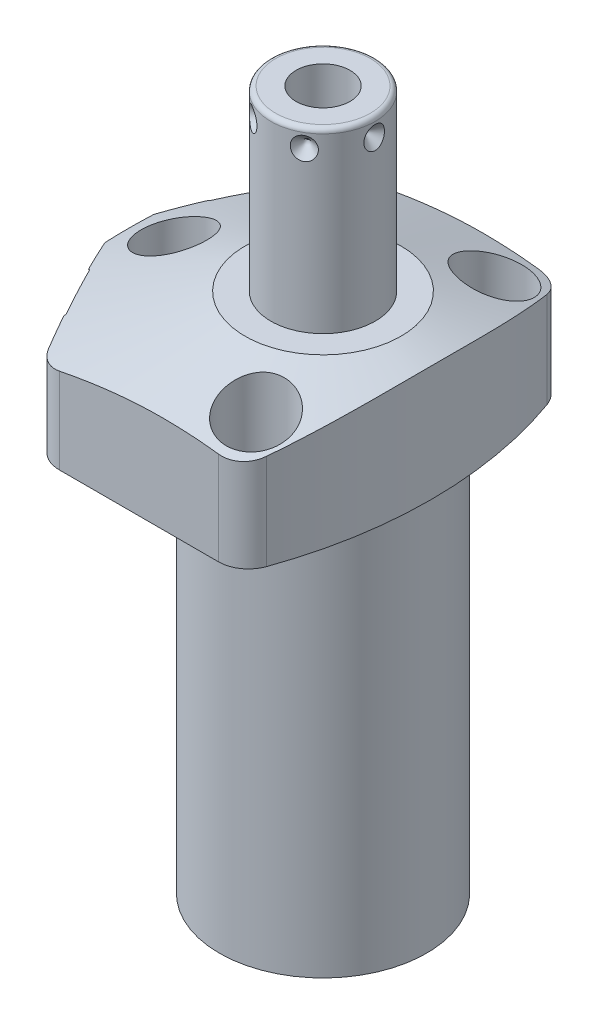
SolidWorks part; units mm, degrees
material "Alloy Steel"
ref_plane "Front Plane" through (0, 0, 0) normal (0, 0, 1) x (1, 0, 0)
ref_plane "Top Plane" through (0, 0, 0) normal (0, 1, 0) x (1, 0, 0)
ref_plane "Right Plane" through (0, 0, 0) normal (1, 0, 0) x (0, 0, -1)
ref_plane "Plane1" through (0, 0, 0) normal (0, 0, 1) x (0, -1, 0)
sketch "Sketch1" plane through (0, 0, 0) normal (0, 0, 1) x (0, -1, 0)
  line L0 (0, 44.45) -> (-26.9748, 44.45)
  line L1 (-26.9748, 44.45) -> (-26.9748, 0)
  line L2 (-26.9748, 0) -> (84.1502, 0)
  line L3 (84.1502, 0) -> (84.1502, 22.098)
  line L4 (84.1502, 22.098) -> (0, 22.098)
  line L5 (0, 22.098) -> (0, 44.45)
  line L6 (-32.531, 0) -> (89.7065, 0) construction
  dimension "D1" = 111.125
  dimension "D2" = 26.9748
  dimension "D3" = 88.9
  dimension "D4" = 44.196
revolve "Revolve1" add sketch "Sketch1" angle 360 about L6
ref_plane "Plane2" through (0, 0, 0) normal (0, -1, 0) x (0, 0, -1)
sketch "Sketch2" plane through (0, 0, 0) normal (0, -1, 0) x (0, 0, -1)
  line L0 (34.1122, -28.4984) -> (34.1122, 28.4984)
  line L2 (-34.1122, 28.4984) -> (-34.1122, -28.4984)
  line L3 (0, -32.1458) -> (0, 48.0974) construction
  arc A0 (34.1122, -28.4984) -> (34.1122, 28.4984) centre (0, 0) ccw
  circle A1 centre (0, 0) radius 44.45
  arc A2 (-34.1122, 28.4984) -> (-34.1122, -28.4984) centre (0, 0) ccw
  point P4 (0, 0)
  dimension "D1" = 68.2244
  dimension "D2" = 0
extrude "Cut-Extrude1" cut sketch "Sketch2" against normal up to next
ref_plane "Plane3" through (0, 0, 0) normal (0, -1, 0) x (-1, 0, 0)
sketch "Sketch3" plane through (0, 0, 0) normal (0, -1, 0) x (-1, 0, 0)
  line L0 (25.9049, 34.1122) -> (44.0427, 0)
  line L1 (44.0427, 0) -> (25.9049, -34.1122)
  line L2 (-39.4859, -20.995) -> (73.8214, 39.2515) construction
  line L3 (0, 0) -> (44.0427, 0) construction
  line L6 (-28.4984, -34.1122) -> (28.4984, -34.1122)
  line L7 (28.4984, 34.1122) -> (-28.4984, 34.1122)
  line L8 (25.9049, -34.1122) -> (28.4984, -34.1122)
  line L9 (28.4984, 34.1122) -> (25.9049, 34.1122)
  arc A2 (-28.4984, 34.1122) -> (-28.4984, -34.1122) centre (0, 0) ccw
  arc A3 (28.4984, -34.1122) -> (28.4984, 34.1122) centre (0, 0) ccw
  arc A5 (28.4984, -34.1122) -> (28.4984, 34.1122) centre (0, 0) ccw
  dimension "D1" = 28
  dimension "D2" = 38.8874
  dimension "D3" = 0
extrude "Cut-Extrude2" cut sketch "Sketch3" against normal up to next
ref_plane "Plane4" through (0, 0, 0) normal (0, -1, 0) x (-1, 0, 0)
sketch "S2D0002" plane through (0, 0, 0) normal (0, -1, 0) x (-1, 0, 0)
  line L0 (41.275, 85.425) -> (41.275, -85.425)
  arc A0 (41.275, 85.425) -> (41.275, -85.425) centre (65.8876, 0) ccw
  dimension "D3" = 88.9
  dimension "D1" = 65.8876
  dimension "D2" = 41.275
extrude "Cut-Extrude3" cut sketch "S2D0002" against normal blind 38.0873 flip side to cut
fillet "Fillet1" radius 6.35 2 edges at (16.2073, 13.4874, 34.1122) (16.2073, 13.4874, -34.1122)
fillet "Fillet2" radius 6.35 1 edges at (-25.9049, 13.4874, 34.1122)
fillet "Fillet3" radius 6.35 1 edges at (-25.9049, 13.4874, -34.1122)
ref_plane "Plane5" through (0, 0, 0) normal (0, 0, 1) x (1, 0, 0)
sketch "Sketch5" plane through (0, 0, 0) normal (0, 0, 1) x (1, 0, 0)
  line L0 (-16.637, 26.9748) -> (-47.625, 15.6961)
  line L1 (0, 7.6649) -> (0, 27.5963) construction
  line L3 (11.854, 26.9748) -> (-22.0895, 26.9748) construction
  line L4 (-16.637, 26.9748) -> (-47.625, 26.9748)
  line L5 (-47.625, 26.9748) -> (-47.625, 15.6961)
  dimension "D1" = 33.274
  dimension "D2" = 20
  dimension "D3" = 47.625
revolve "Cut-Revolve1" cut sketch "Sketch5" angle 360 about L1
ref_plane "Plane6" through (-34.1113, 10.287, -18.1373) normal (0, 1, 0) x (0.4695, 0, -0.8829)
sketch "Sketch6" plane through (-34.1113, 10.287, -18.1373) normal (0, 1, 0) x (0.4695, 0, -0.8829)
  line L0 (0, 0) -> (6.1849, 0)
  line L1 (6.1849, 0) -> (5.6423, -2.5527)
  line L2 (5.6423, -2.5527) -> (4.9784, -3.2166)
  line L3 (4.9784, -3.2166) -> (4.9784, -15.748)
  line L4 (4.9784, -15.748) -> (0, -15.748)
  line L5 (0, -15.748) -> (0, 0)
  line L6 (0, -16.5354) -> (0, 0.7874) construction
  dimension "D1" = 15.748
revolve "Cut-Revolve2" cut sketch "Sketch6" angle 360 about L6
ref_plane "Plane7" through (-34.1113, 10.287, 18.1373) normal (0, 1, 0) x (-0.4695, 0, -0.8829)
sketch "Sketch7" plane through (-34.1113, 10.287, 18.1373) normal (0, 1, 0) x (-0.4695, 0, -0.8829)
  line L0 (0, 0) -> (6.1849, 0)
  line L1 (6.1849, 0) -> (5.6423, -2.5527)
  line L2 (5.6423, -2.5527) -> (4.9784, -3.2166)
  line L3 (4.9784, -3.2166) -> (4.9784, -15.748)
  line L4 (4.9784, -15.748) -> (0, -15.748)
  line L5 (0, -15.748) -> (0, 0)
  line L6 (0, -16.5354) -> (0, 0.7874) construction
  dimension "D1" = 15.748
revolve "Cut-Revolve3" cut sketch "Sketch7" angle 360 about L6
ref_plane "Plane8" through (-13.4874, 2.667, -26.5938) normal (0, 0, 1) x (-1, 0, 0)
sketch "Sketch8" plane through (-13.4874, 2.667, -26.5938) normal (0, 0, 1) x (-1, 0, 0)
  line L0 (0, 0) -> (4.5466, 0)
  line L1 (4.5466, 0) -> (4.1066, -2.0701)
  line L2 (4.1066, -2.0701) -> (3.4544, -2.7223)
  line L3 (3.4544, -2.7223) -> (3.4544, -12.573)
  line L4 (3.4544, -12.573) -> (0, -12.573)
  line L5 (0, -12.573) -> (0, 0)
  line L6 (0, -13.2017) -> (0, 0.6287) construction
  dimension "D1" = 12.573
revolve "Cut-Revolve4" cut sketch "Sketch8" angle 360 about L6
ref_plane "Plane9" through (-13.4874, 2.667, 26.5938) normal (0, 0, 1) x (-1, 0, 0)
sketch "Sketch9" plane through (-13.4874, 2.667, 26.5938) normal (0, 0, 1) x (-1, 0, 0)
  line L0 (0, 0) -> (4.5466, 0)
  line L1 (4.5466, 0) -> (4.1066, -2.0701)
  line L2 (4.1066, -2.0701) -> (3.4544, -2.7223)
  line L3 (3.4544, -2.7223) -> (3.4544, -12.573)
  line L4 (3.4544, -12.573) -> (0, -12.573)
  line L5 (0, -12.573) -> (0, 0)
  line L6 (0, -13.2017) -> (0, 0.6287) construction
  dimension "D1" = 12.573
revolve "Cut-Revolve5" cut sketch "Sketch9" angle 360 about L6
sketch "Sketch17" plane through (-34.3355, 0, 18.2565) normal (-0.8829, 0, 0.4695) x (0.4695, 0, 0.8829)
  circle A0 centre (0, 10.287) radius 10.4775
  dimension "D1" = 20.955
extrude "Cut-Extrude4" cut sketch "Sketch17" against normal blind 0.254
sketch "Sketch18" plane through (0, 0, 0) normal (0, -1, 0) x (1, 0, 0)
  circle A0 centre (-13.4874, 26.5938) radius 5.5626
  dimension "D1" = 11.1252
extrude "Cut-Extrude5" cut sketch "Sketch18" against normal blind 2.667
mirror "Mirror1" about plane through (0, 0, 0) normal (0, 0, 1) of "Cut-Extrude5", "Cut-Extrude4"
ref_plane "Plane10" through (0, 0, 0) normal (1, 0, 0) x (0, 0, -1)
sketch "Sketch10" plane through (0, 0, 0) normal (1, 0, 0) x (0, 0, -1)
  line L0 (0, 26.9748) -> (-11.1125, 26.9748)
  line L1 (-11.1125, 26.9748) -> (-11.1125, 63.8302)
  line L2 (-10.0965, 64.8462) -> (0, 64.8462)
  line L3 (0, 64.8462) -> (0, 26.9748)
  line L4 (0, 14.3517) -> (0, 66.7398) construction
  line L5 (16.637, 26.9748) -> (-16.637, 26.9748) construction
  line L6 (-29.8978, 0) -> (29.8978, 0) construction
  arc A0 (-10.0965, 64.8462) -> (-11.1125, 63.8302) centre (-10.0965, 63.8302) ccw
  dimension "D2" = 1.016
  dimension "D1" = 64.8462
  dimension "D3" = 22.225
revolve "Revolve2" add sketch "Sketch10" angle 360 about L4
ref_plane "Plane11" through (5.7531, 64.8462, 0) normal (0, 0, 1) x (1, 0, 0)
sketch "S2D0001" plane through (5.7531, 64.8462, 0) normal (0, 0, 1) x (1, 0, 0)
  line L0 (0, 0) -> (0, -17.018)
  line L1 (0, -17.018) -> (-5.7531, -20.4748)
  line L2 (0, 0) -> (-5.7531, 0)
  line L3 (-5.7531, 0) -> (-5.7531, -20.4748)
  line L4 (-5.7531, -27.7363) -> (-5.7531, 1.0237) construction
  line L5 (4.3434, 0) -> (-15.8496, 0) construction
  dimension "D1" = 11.5062
  dimension "D2" = 17.018
  dimension "D3" = 59
revolve "Cut-Revolve6" cut sketch "S2D0001" angle 360 about L4
sketch "Sketch12" plane through (-34.1113, 0, -18.1373) normal (-0.8829, 0, -0.4695) x (-0.4695, 0, 0.8829)
  circle A0 centre (0, 10.287) radius 6.4389
  circle A1 centre (0, 10.287) radius 4.9784 construction
  dimension "D1" = 12.8778
extrude "Extrude1" add sketch "Sketch12" along normal blind 1.651
sketch "Sketch13" plane through (0, 0, 0) normal (0, -1, 0) x (1, 0, 0)
  circle A0 centre (-13.4874, -26.5938) radius 4.8006
  circle A1 centre (-13.4874, -26.5938) radius 3.4544 construction
  dimension "D1" = 9.6012
ref_plane "Plane12" through (-13.4874, 2.667, -26.5938) normal (0, 1, 0) x (-1, 0, 0)
extrude "Extrude2" add sketch "Sketch13" against normal up to surface
ref_plane "Plane13" through (-13.4874, 0, 26.5938) normal (1, 0, 0) x (0, 0, -1)
sketch "Sketch14" plane through (-13.4874, 0, 26.5938) normal (1, 0, 0) x (0, 0, -1)
  line L0 (5.461, 2.667) -> (5.461, 0.9398)
  line L1 (5.461, 0.9398) -> (5.3016, 0.9398)
  line L2 (2.667, 0.4318) -> (2.667, 0.127)
  line L3 (2.667, 0.127) -> (1.5875, 0.127)
  line L4 (1.5875, 0.127) -> (1.5875, 10.6172)
  line L5 (1.5875, 10.6172) -> (3.2512, 10.6172)
  line L6 (3.2512, 10.6172) -> (3.2512, 2.667)
  line L7 (3.2512, 2.667) -> (5.461, 2.667)
  line L8 (3.175, 0.9398) -> (3.8424, 0.9398)
  line L9 (0, -1.0109) -> (0, 11.1709) construction
  arc A0 (3.175, 0.9398) -> (2.667, 0.4318) centre (3.175, 0.4318) ccw
  arc A1 (3.8424, 0.9398) -> (5.3016, 0.9398) centre (4.572, 0.4318) ccw
  dimension "D1" = 2.54
  dimension "D2" = 7.9502
revolve "Revolve3" add sketch "Sketch14" angle 360 about L9
ref_plane "Plane14" through (-11.1125, 60.8838, 0) normal (0, 0, 1) x (0, 1, 0)
sketch "Sketch15" plane through (-11.1125, 60.8838, 0) normal (0, 0, 1) x (0, 1, 0)
  line L0 (0, 0) -> (2.413, 0)
  line L1 (2.413, 0) -> (0, -2.413)
  line L2 (0, 0) -> (0, -2.413)
  line L3 (0, -5.1094) -> (0, 0.1207) construction
  line L4 (2.9464, 0) -> (-33.909, 0) construction
  line L5 (3.9624, -21.209) -> (3.9624, -1.016) construction
  dimension "D1" = 3.9624
  dimension "D2" = 4.826
  dimension "D3" = 45
revolve "Cut-Revolve7" cut sketch "Sketch15" angle 360 about L3
pattern_circular "CirPattern1" count 6 over 360 about axis through (0, 14.3517, 0) along (0, -1, 0) of "Cut-Revolve7"
hole_wizard "Hole1" positions "Sketch20" profile "Sketch19" legacy end condition up to next
sketch "Sketch20" plane through (0, 26.9748, 0) normal (0, 1, 0) x (-1, 0, 0)
  line L0 (0, 0) -> (47.6205, 0) construction
  line L1 (0, 0) -> (0, 38.9977) construction
  point P0 (-11.1252, -25.4)
  point P10 (31.75, 0)
  point P14 (-11.1252, 25.4)
  dimension "D1" = 11.1252
  dimension "D2" = 25.4
  dimension "D3" = 31.75
sketch "Sketch19" plane through (11.1252, 26.9748, -25.4) normal (1, 0, 0) x (0, 0, 1)
  line L0 (0, 0) -> (0, 26.9748)
  line L1 (0, 26.9748) -> (4.3688, 26.9748)
  line L2 (4.3688, 26.9748) -> (4.3688, 16.6624)
  line L3 (4.3688, 16.6624) -> (6.9977, 16.6624)
  line L4 (6.9977, 16.6624) -> (6.9977, 0)
  line L5 (6.9977, 0) -> (0, 0)
  line L6 (0, 110) -> (0, -10) construction
  dimension "Diameter" = 8.7376
  dimension "Depth" = 26.9748
  dimension "C-Bore Diameter" = 13.9954
  dimension "C-Bore Depth" = 16.6624
